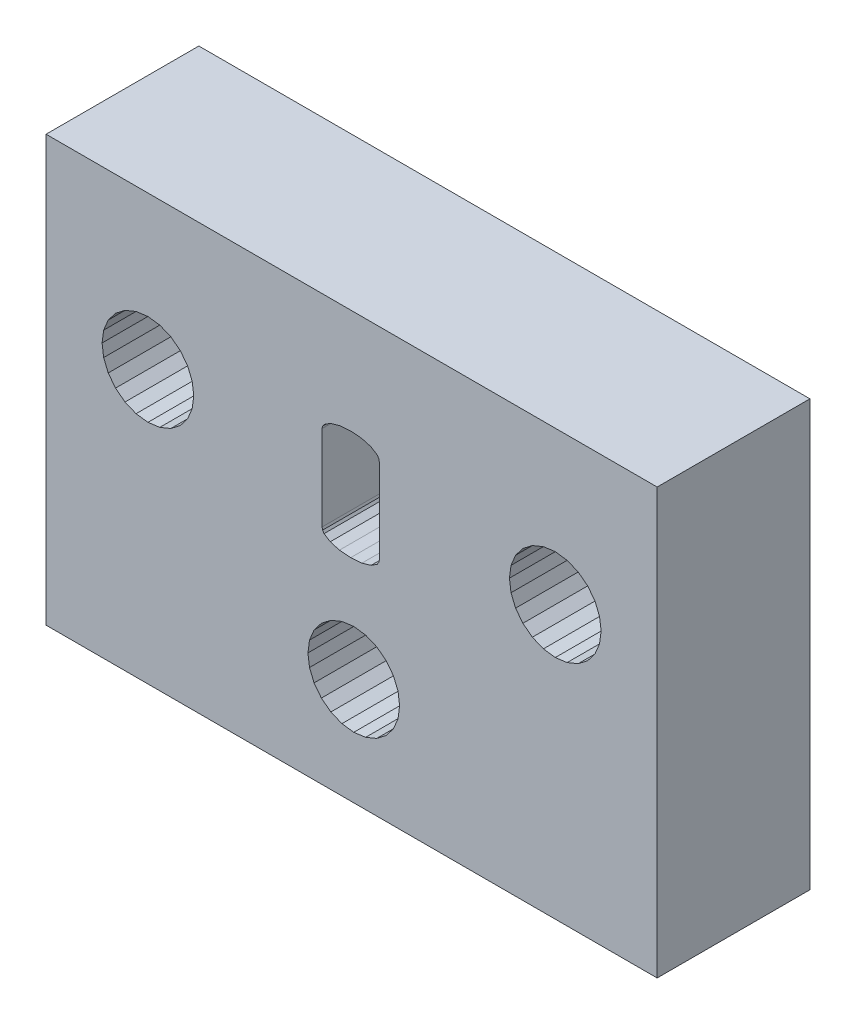
SolidWorks part; units mm, degrees
material "Maple"
ref_plane "Front Plane" through (0, 0, 0) normal (0, 0, 1) x (1, 0, 0)
ref_plane "Top Plane" through (0, 0, 0) normal (0, 1, 0) x (1, 0, 0)
ref_plane "Right Plane" through (0, 0, 0) normal (1, 0, 0) x (0, 0, -1)
sketch "Sketch1" plane through (0, 0, 0) normal (0, 0, 1) x (1, 0, 0)
  line L7160 (240.9387, 76.4348) -> (264.9387, 76.4348)
  line L7161 (240.9387, 59.7348) -> (240.9387, 76.4348)
  line L7162 (264.9387, 76.4348) -> (264.9387, 59.7348)
  line L7163 (264.9387, 59.7348) -> (240.9387, 59.7348)
  line L7164 (260.4717, 68.6961) -> (260.9376, 68.6348)
  line L7165 (243.6659, 69.162) -> (244.0387, 68.8759)
  line L7166 (260.9376, 68.6348) -> (261.4035, 68.6961)
  line L7167 (262.4964, 71.3348) -> (262.2104, 71.7076)
  line L7168 (262.6762, 70.9007) -> (262.4964, 71.3348)
  line L7169 (243.2, 70.9007) -> (243.1387, 70.4348)
  line L7170 (262.2104, 69.162) -> (262.4964, 69.5348)
  line L7171 (244.9387, 72.2348) -> (244.4728, 72.1735)
  line L7172 (261.4035, 68.6961) -> (261.8376, 68.8759)
  line L7173 (251.4646, 63.0348) -> (251.7507, 62.662)
  line L7174 (253.0235, 65.7348) -> (252.5576, 65.6735)
  line L7175 (251.2235, 63.9348) -> (251.2848, 63.4689)
  line L7176 (253.0235, 62.1348) -> (253.4893, 62.1961)
  line L7177 (253.9235, 65.4936) -> (253.4893, 65.6735)
  line L7178 (251.7507, 62.662) -> (252.1235, 62.376)
  line L7179 (252.5576, 62.1961) -> (253.0235, 62.1348)
  line L7180 (253.4893, 65.6735) -> (253.0235, 65.7348)
  line L7181 (251.2848, 64.4007) -> (251.2235, 63.9348)
  line L7182 (251.2848, 63.4689) -> (251.4646, 63.0348)
  line L7183 (253.4893, 62.1961) -> (253.9235, 62.376)
  line L7184 (254.7621, 64.4007) -> (254.5823, 64.8348)
  line L7185 (252.1235, 62.376) -> (252.5576, 62.1961)
  line L7186 (252.5576, 65.6735) -> (252.1235, 65.4936)
  line L7187 (254.2963, 62.662) -> (254.5823, 63.0348)
  line L7188 (262.4964, 69.5348) -> (262.6762, 69.9689)
  line L7189 (243.3799, 69.5348) -> (243.6659, 69.162)
  line L7190 (261.8376, 68.8759) -> (262.2104, 69.162)
  line L7191 (246.7387, 70.4348) -> (246.6774, 70.9007)
  line L7192 (246.4975, 69.5348) -> (246.6774, 69.9689)
  line L7193 (262.2104, 71.7076) -> (261.8376, 71.9936)
  line L7194 (244.4728, 68.6961) -> (244.9387, 68.6348)
  line L7195 (259.1989, 69.9689) -> (259.3787, 69.5348)
  line L7196 (245.4046, 68.6961) -> (245.8387, 68.8759)
  line L7197 (246.6774, 70.9007) -> (246.4975, 71.3348)
  line L7198 (244.4728, 72.1735) -> (244.0387, 71.9936)
  line L7199 (253.9235, 62.376) -> (254.2963, 62.662)
  line L7200 (261.4035, 72.1735) -> (260.9376, 72.2348)
  line L7201 (260.9376, 72.2348) -> (260.4717, 72.1735)
  line L7202 (245.8387, 71.9936) -> (245.4046, 72.1735)
  line L7203 (243.6659, 71.7076) -> (243.3799, 71.3348)
  line L7204 (259.1989, 70.9007) -> (259.1376, 70.4348)
  line L7205 (254.5823, 64.8348) -> (254.2963, 65.2076)
  line L7206 (259.6648, 69.162) -> (260.0376, 68.8759)
  line L7207 (251.4646, 64.8348) -> (251.2848, 64.4007)
  line L7208 (254.8235, 63.9348) -> (254.7621, 64.4007)
  line L7209 (246.2115, 71.7076) -> (245.8387, 71.9936)
  line L7210 (251.7507, 65.2076) -> (251.4646, 64.8348)
  line L7211 (244.9387, 68.6348) -> (245.4046, 68.6961)
  line L7212 (254.2963, 65.2076) -> (253.9235, 65.4936)
  line L7213 (244.0387, 68.8759) -> (244.4728, 68.6961)
  line L7214 (259.1376, 70.4348) -> (259.1989, 69.9689)
  line L7215 (260.4717, 72.1735) -> (260.0376, 71.9936)
  line L7216 (252.1235, 65.4936) -> (251.7507, 65.2076)
  line L7217 (254.7621, 63.4689) -> (254.8235, 63.9348)
  line L7218 (261.8376, 71.9936) -> (261.4035, 72.1735)
  line L7219 (246.6774, 69.9689) -> (246.7387, 70.4348)
  line L7220 (243.2, 69.9689) -> (243.3799, 69.5348)
  line L7221 (244.0387, 71.9936) -> (243.6659, 71.7076)
  line L7222 (245.8387, 68.8759) -> (246.2115, 69.162)
  line L7223 (259.3787, 69.5348) -> (259.6648, 69.162)
  line L7224 (259.3787, 71.3348) -> (259.1989, 70.9007)
  line L7225 (262.6762, 69.9689) -> (262.7376, 70.4348)
  line L7226 (246.2115, 69.162) -> (246.4975, 69.5348)
  line L7227 (245.4046, 72.1735) -> (244.9387, 72.2348)
  line L7228 (243.1387, 70.4348) -> (243.2, 69.9689)
  line L7229 (259.6648, 71.7076) -> (259.3787, 71.3348)
  line L7230 (262.7376, 70.4348) -> (262.6762, 70.9007)
  line L7231 (246.4975, 71.3348) -> (246.2115, 71.7076)
  line L7232 (243.3799, 71.3348) -> (243.2, 70.9007)
  line L7233 (260.0376, 71.9936) -> (259.6648, 71.7076)
  line L7234 (260.0376, 68.8759) -> (260.4717, 68.6961)
  line L7235 (254.5823, 63.0348) -> (254.7621, 63.4689)
  line L9566 (251.7779, 68.494) -> (251.798, 68.3978)
  line L9567 (251.798, 68.3978) -> (251.8583, 68.309)
  line L9568 (251.8583, 68.309) -> (252.0994, 68.1537)
  line L9569 (252.0994, 68.1537) -> (252.4608, 68.0483)
  line L9570 (252.4608, 68.0483) -> (252.9018, 68.0132)
  line L9571 (252.9018, 68.0132) -> (253.3428, 68.0483)
  line L9572 (253.3428, 68.0483) -> (253.7041, 68.1537)
  line L9573 (253.7041, 68.1537) -> (253.9453, 68.309)
  line L9574 (253.9453, 68.309) -> (254.0056, 68.3978)
  line L9575 (254.0056, 68.3978) -> (254.0257, 68.494)
  line L9576 (254.0257, 68.494) -> (254.0257, 71.8404)
  line L9577 (254.0257, 71.8404) -> (254.0056, 71.9366)
  line L9578 (254.0056, 71.9366) -> (253.9453, 72.0253)
  line L9579 (253.9453, 72.0253) -> (253.7041, 72.1806)
  line L9580 (253.7041, 72.1806) -> (253.3428, 72.286)
  line L9581 (253.3428, 72.286) -> (252.9018, 72.3211)
  line L9582 (252.9018, 72.3211) -> (252.4608, 72.286)
  line L9583 (252.4608, 72.286) -> (252.0994, 72.1806)
  line L9584 (252.0994, 72.1806) -> (251.8583, 72.0253)
  line L9585 (251.8583, 72.0253) -> (251.798, 71.9366)
  line L9586 (251.798, 71.9366) -> (251.7779, 71.8404)
  line L9587 (251.7779, 71.8404) -> (251.7779, 68.494)
  line L9588 (254.0257, 68.494) -> (254.0056, 68.3978)
  line L9589 (254.0056, 68.3978) -> (253.9453, 68.309)
  line L9590 (253.9453, 68.309) -> (253.7041, 68.1537)
  line L9591 (253.7041, 68.1537) -> (253.3428, 68.0483)
  line L9592 (253.3428, 68.0483) -> (252.9018, 68.0132)
  line L9593 (252.9018, 68.0132) -> (252.4608, 68.0483)
  line L9594 (252.4608, 68.0483) -> (252.0994, 68.1537)
  line L9595 (252.0994, 68.1537) -> (251.8583, 68.309)
  line L9596 (251.8583, 68.309) -> (251.798, 68.3978)
  line L9597 (251.798, 68.3978) -> (251.7779, 68.494)
  line L9598 (251.7779, 68.494) -> (251.7779, 71.8404)
  line L9599 (251.7779, 71.8404) -> (251.798, 71.9366)
  line L9600 (251.798, 71.9366) -> (251.8583, 72.0253)
  line L9601 (251.8583, 72.0253) -> (252.0994, 72.1806)
  line L9602 (252.0994, 72.1806) -> (252.4608, 72.286)
  line L9603 (252.4608, 72.286) -> (252.9018, 72.3211)
  line L9604 (252.9018, 72.3211) -> (253.3428, 72.286)
  line L9605 (253.3428, 72.286) -> (253.7041, 72.1806)
  line L9606 (253.7041, 72.1806) -> (253.9453, 72.0253)
  line L9607 (253.9453, 72.0253) -> (254.0056, 71.9366)
  line L9608 (254.0056, 71.9366) -> (254.0257, 71.8404)
  line L9609 (254.0257, 71.8404) -> (254.0257, 68.494)
extrude "Boss-Extrude1" add sketch "Sketch1" along normal blind 6 contours L7163 L7162 L7160 L7161 L9587 L9586 L9585 L9584 L9583 L9582 L9581 L9580 L9579 L9578 L9577 L9576 L9575 L9574 L9573 L9572 L9571 L9570 L9569 L9568 L9567 L9566 L7235 L7187 L7199 L7183 L7176 L7179 L7185 L7178 L7173 L7182 L7175 L7181 L7207 L7210 L7216 L7186 L7174 L7180 L7177 L7212 L7205 L7184 L7208
